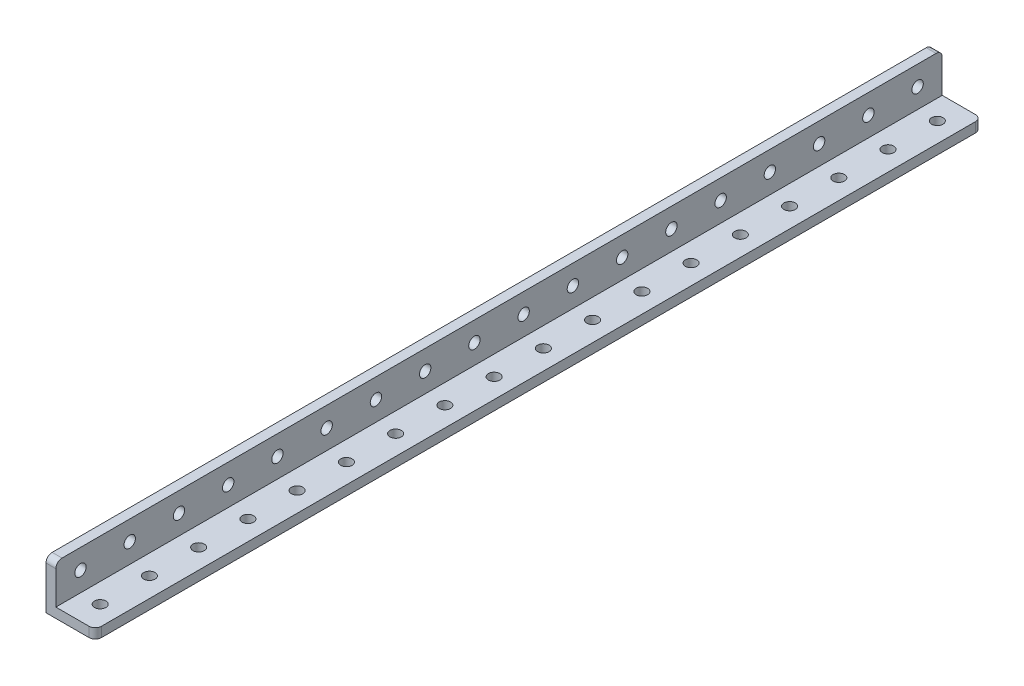
SolidWorks part; units mm, degrees
material "2024 Alloy"
ref_plane "Front Plane" through (0, 0, 0) normal (0, 0, 1) x (1, 0, 0)
ref_plane "Top Plane" through (0, 0, 0) normal (0, 1, 0) x (1, 0, 0)
ref_plane "Right Plane" through (0, 0, 0) normal (1, 0, 0) x (0, 0, -1)
ref_plane "Plane1" through (0, 16, 0) normal (0, 1, 0) x (1, 0, 0)
sketch "Sketch1" plane through (0, 16, 0) normal (0, 1, 0) x (1, 0, 0)
  line L0 (0, 0) -> (16, 0)
  line L1 (16, 0) -> (16, 288)
  line L2 (16, 288) -> (0, 288)
  line L3 (0, 288) -> (0, 0)
extrude "Boss-Extrude1" add sketch "Sketch1" against normal blind 16
sketch "Sketch2" plane through (0, 0, -288) normal (0, 0, -1) x (-1, 0, 0)
  line L0 (-16, 3.2) -> (-3.2, 3.2)
  line L1 (-3.2, 3.2) -> (-3.2, 16)
  line L2 (-3.2, 16) -> (-16, 16)
  line L3 (-16, 16) -> (-16, 3.2)
extrude "Cut-Extrude1" cut sketch "Sketch2" against normal through all
hole_wizard "Ø3.7 (3.7) Diameter Hole1" positions "Sketch4" profile "Sketch3" hole size "Ø3.7" standard "ANSI Metric"
sketch "Sketch4" plane through (0, 0, 0) normal (0, -1, 0) x (-1, 0, 0)
  point P0 (-9.6, 24)
  point P1 (-9.6, 40)
  point P2 (-9.6, 56)
  point P3 (-9.6, 72)
  point P4 (-9.6, 88)
  point P5 (-9.6, 104)
  point P6 (-9.6, 120)
  point P7 (-9.6, 136)
  point P8 (-9.6, 152)
  point P9 (-9.6, 168)
  point P10 (-9.6, 184)
  point P11 (-9.6, 200)
  point P12 (-9.6, 216)
  point P13 (-9.6, 232)
  point P14 (-9.6, 248)
  point P15 (-9.6, 264)
  point P16 (-9.6, 280)
  point P17 (-9.6, 8)
sketch "Sketch3" plane through (9.6, 0, -24) normal (1, 0, 0) x (0, 0, -1)
  line L0 (0, 0) -> (0, 16)
  line L1 (0, 16) -> (1.85, 16)
  line L2 (1.85, 16) -> (1.85, 0)
  line L5 (1.85, 0) -> (0, 0)
  line L11 (0, -6.35) -> (0, 107.95) construction
  dimension "Thru Hole Dia." = 3.7
  dimension "Thru Hole Depth" = 16
hole_wizard "Ø3.7 (3.7) Diameter Hole2" positions "Sketch6" profile "Sketch5" hole size "Ø3.7" standard "ANSI Metric"
sketch "Sketch6" plane through (0, 0, 0) normal (-1, 0, 0) x (0, 0, 1)
  point P0 (-24, 9.6)
  point P1 (-40, 9.6)
  point P2 (-56, 9.6)
  point P3 (-72, 9.6)
  point P4 (-88, 9.6)
  point P5 (-104, 9.6)
  point P6 (-120, 9.6)
  point P7 (-136, 9.6)
  point P8 (-152, 9.6)
  point P9 (-168, 9.6)
  point P10 (-184, 9.6)
  point P11 (-200, 9.6)
  point P12 (-216, 9.6)
  point P13 (-232, 9.6)
  point P14 (-248, 9.6)
  point P15 (-264, 9.6)
  point P16 (-280, 9.6)
  point P17 (-8, 9.6)
sketch "Sketch5" plane through (0, 9.6, -24) normal (0, 1, 0) x (0, 0, 1)
  line L0 (0, 0) -> (0, 16)
  line L1 (0, 16) -> (1.85, 16)
  line L2 (1.85, 16) -> (1.85, 0)
  line L5 (1.85, 0) -> (0, 0)
  line L11 (0, -6.35) -> (0, 107.95) construction
  dimension "Thru Hole Dia." = 3.7
  dimension "Thru Hole Depth" = 16
fillet "Fillet1" radius 2 4 edges at (16, 1.6, -288) (16, 1.6, 0) (1.6, 16, 0) (1.6, 16, -288)
